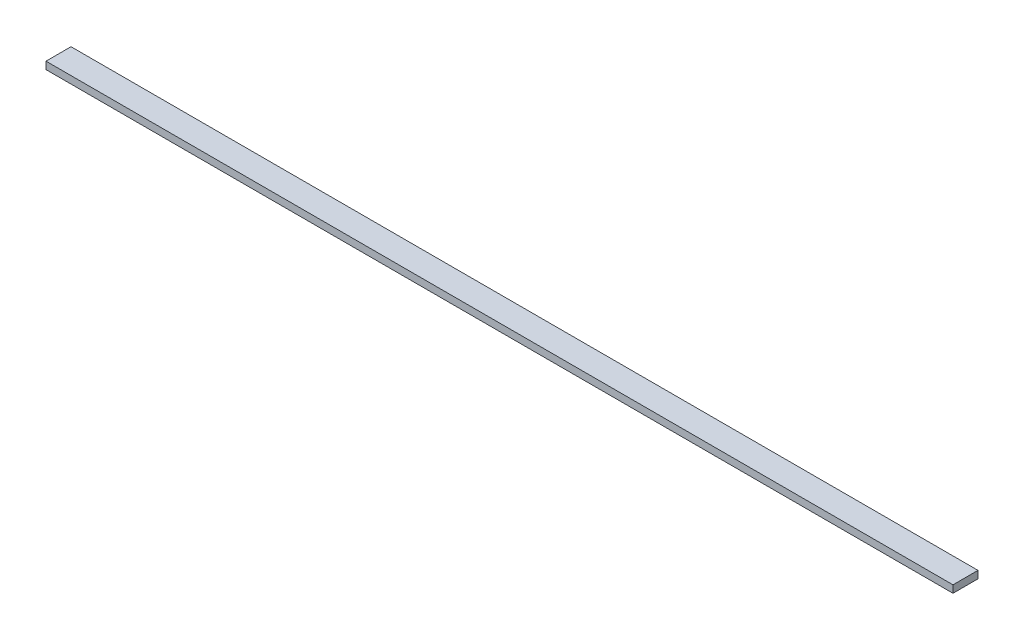
SolidWorks part; units mm, degrees
ref_plane "Plano frontal" through (0, 0, 0) normal (0, 0, 1) x (1, 0, 0)
ref_plane "Plano superior" through (0, 0, 0) normal (0, 1, 0) x (1, 0, 0)
ref_plane "Plano direito" through (0, 0, 0) normal (1, 0, 0) x (0, 0, -1)
sketch "Sketch3" plane through (0, 0, 0) normal (0, 1, 0) x (1, 0, 0)
  line L1 (-61.625, 1.7) -> (61.625, 1.7)
  line L2 (-61.625, 1.7) -> (-61.625, -1.7)
  line L3 (-61.625, -1.7) -> (61.625, -1.7)
  line L4 (61.625, 1.7) -> (61.625, -1.7)
  point P4 (61.625, 0)
  point P6 (0, 1.7)
  dimension "D1" = 3.4
  dimension "D2" = 123.25
extrude "Boss-Extrude3" add sketch "Sketch3" along normal mid plane 1
